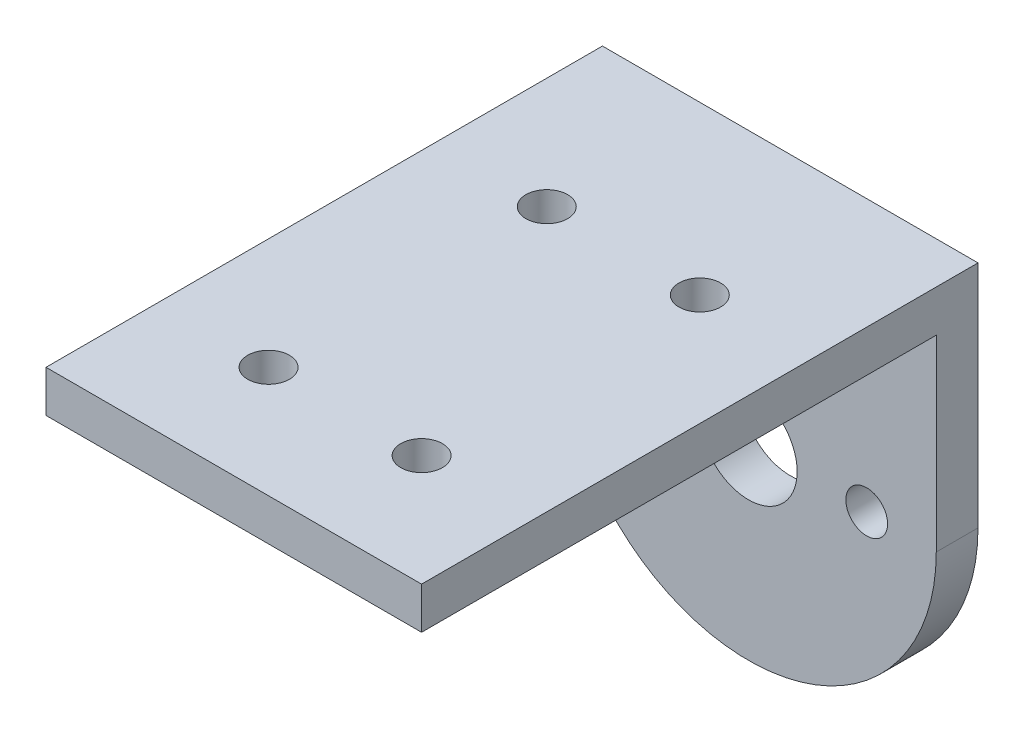
SolidWorks part; units mm, degrees
ref_plane "前视基准面" through (0, 0, 0) normal (0, 0, 1) x (1, 0, 0)
ref_plane "上视基准面" through (0, 0, 0) normal (0, 1, 0) x (1, 0, 0)
ref_plane "右视基准面" through (0, 0, 0) normal (1, 0, 0) x (0, 0, -1)
sketch "Model" plane through (0, 0, 0) normal (0, 0, 1) x (1, 0, 0)
  line L0 (2619.7667, 1592.8264) -> (2619.7667, 1609.3264)
  line L1 (2592.7667, 1592.8264) -> (2592.7667, 1609.3264)
  line L2 (2592.7667, 1609.3264) -> (2619.7667, 1609.3264)
  circle A0 centre (2606.2667, 1592.8264) radius 3.5
  arc A1 (2592.7667, 1592.8264) -> (2619.7667, 1592.8264) centre (2606.2667, 1592.8264) ccw
  dimension "D1" = 16.5
extrude "凸台-拉伸1" add sketch "Model" along normal blind 40
sketch "草图3" plane through (2619.7667, 0, 0) normal (1, 0, 0) x (0, 0, -1)
  line L0 (-40, 1592.8264) -> (-40, 1609.3264) construction
  line L1 (-40, 1606.3264) -> (-3, 1606.3264)
  line L2 (-40, 1606.3264) -> (-40, 1569.3264)
  line L3 (-40, 1569.3264) -> (-3, 1569.3264)
  line L4 (-3, 1606.3264) -> (-3, 1569.3264)
  line L5 (-40, 1609.3264) -> (0, 1609.3264) construction
  line L6 (0, 1592.8264) -> (0, 1609.3264) construction
  dimension "D1" = 3
  dimension "D2" = 3
  dimension "D3" = 40
extrude "切除-拉伸1" cut sketch "草图3" against normal blind 40
sketch "草图4" plane through (0, 1609.3264, 0) normal (0, 1, 0) x (1, 0, 0)
  line L6 (2619.7667, -40) -> (2619.7667, -32)
  circle A0 centre (2600.7667, -32) radius 1.5
  circle A1 centre (2611.7667, -32) radius 1.5
  circle A2 centre (2600.7667, -12) radius 1.5
  circle A3 centre (2611.7667, -12) radius 1.5
  dimension "D7" = 3
  dimension "D8" = 3
  dimension "D9" = 3
  dimension "D10" = 3
extrude "切除-拉伸2" cut sketch "草图4" against normal blind 40 contours A0 | A1 | A3 | A2
sketch "Sketch2" plane through (0, 0, 0) normal (0, 0, -1) x (-1, 0, 0)
  circle A4 centre (-2597.7667, 1592.8264) radius 1.5
  circle A5 centre (-2614.7667, 1592.8264) radius 1.5
extrude "Cut-Extrude1" cut sketch "Sketch2" against normal up to next
